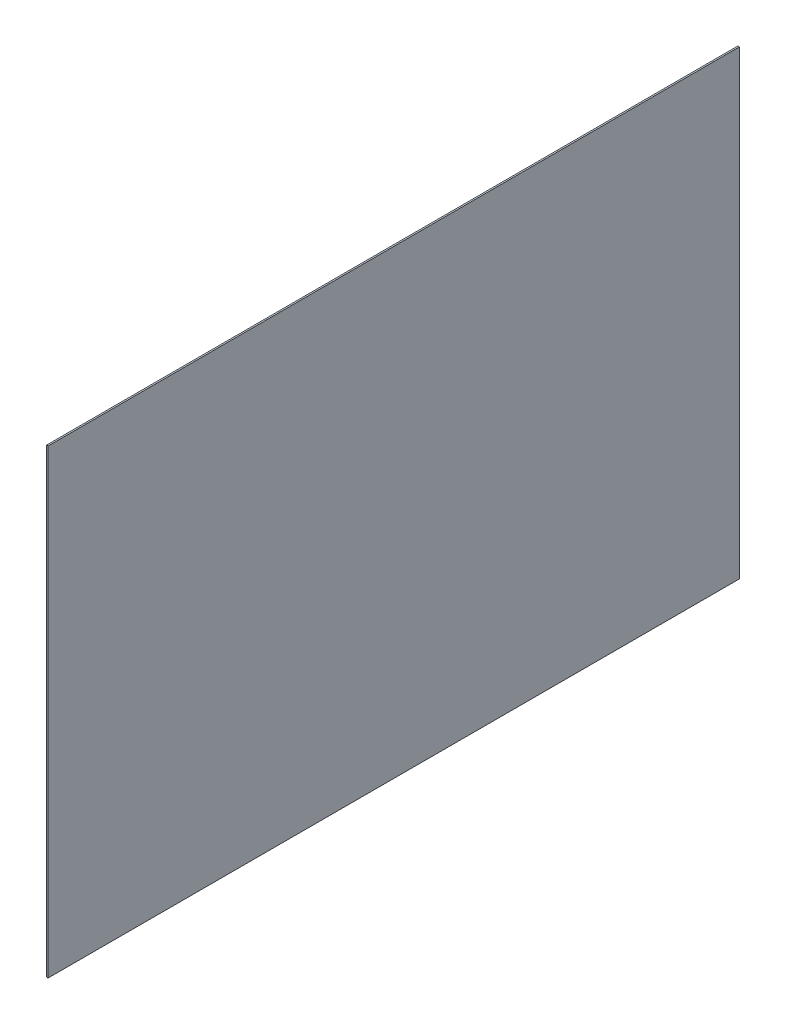
SolidWorks part; units mm, degrees
material "1023 Carbon Steel Sheet (SS)"
ref_plane "Front Plane" through (0, 0, 0) normal (0, 0, 1) x (1, 0, 0)
ref_plane "Top Plane" through (0, 0, 0) normal (0, 1, 0) x (1, 0, 0)
ref_plane "Right Plane" through (0, 0, 0) normal (1, 0, 0) x (0, 0, -1)
sketch "Sketch1" plane through (0, 0, 0) normal (1, 0, 0) x (0, 0, -1)
  line L1 (-225, 150) -> (225, 150)
  line L2 (-225, 150) -> (-225, -150)
  line L3 (-225, -150) -> (225, -150)
  line L4 (225, 150) -> (225, -150)
  line L5 (-225, 150) -> (225, -150) construction
  line L6 (-225, -150) -> (225, 150) construction
  point P0 (0, 0)
  dimension "D1" = 300
  dimension "D2" = 450
extrude "Boss-Extrude1" add sketch "Sketch1" along normal blind 1
